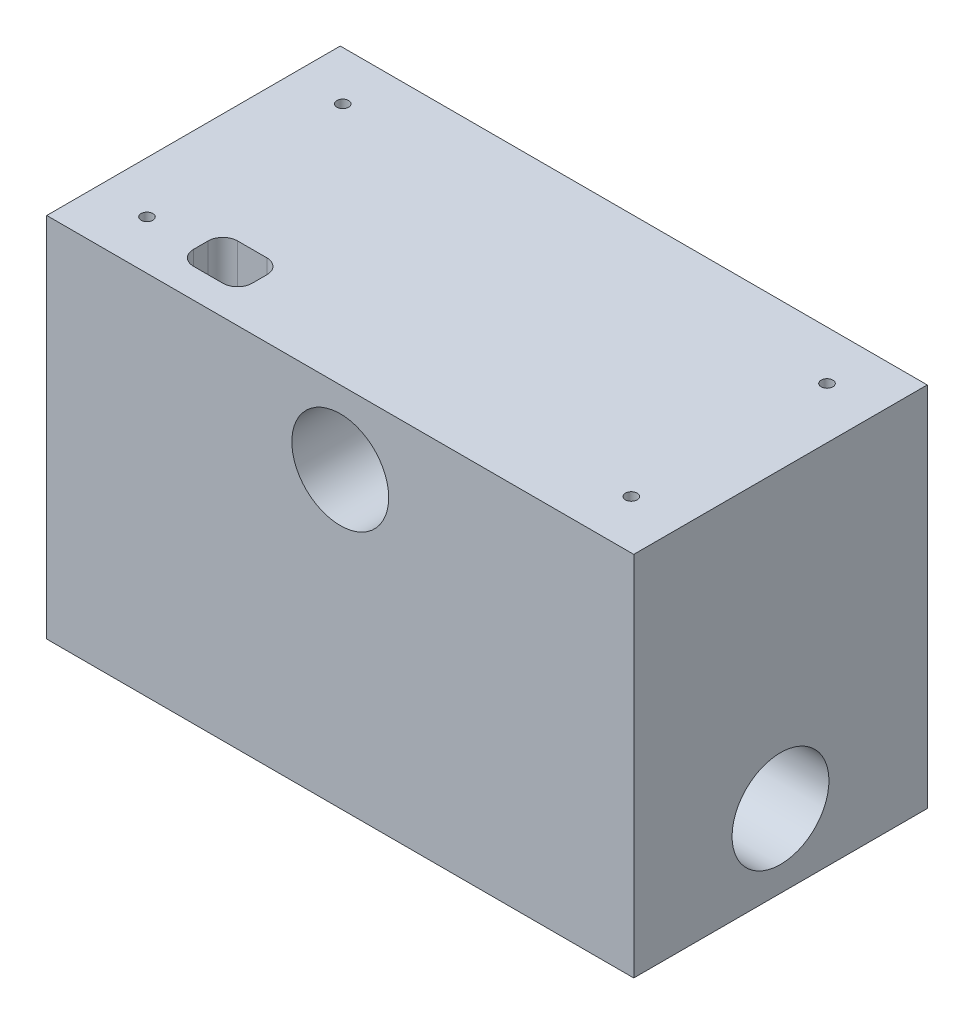
SolidWorks part; units mm, degrees
ref_plane "Front Plane" through (0, 0, 0) normal (0, 0, 1) x (1, 0, 0)
ref_plane "Top Plane" through (0, 0, 0) normal (0, 1, 0) x (1, 0, 0)
ref_plane "Right Plane" through (0, 0, 0) normal (1, 0, 0) x (0, 0, -1)
sketch "Sketch1" plane through (0, 0, 0) normal (0, 0, 1) x (1, 0, 0)
  line L1 (-25.4, 15.875) -> (25.4, 15.875)
  line L2 (-25.4, 15.875) -> (-25.4, -15.875)
  line L3 (-25.4, -15.875) -> (25.4, -15.875)
  line L4 (25.4, 15.875) -> (25.4, -15.875)
  line L5 (-25.4, 15.875) -> (25.4, -15.875) construction
  line L6 (-25.4, -15.875) -> (25.4, 15.875) construction
  point P0 (0, 0)
  dimension "D1" = 50.8
  dimension "D2" = 31.75
extrude "Boss-Extrude1" add sketch "Sketch1" along normal blind 25.4
sketch "Sketch4" plane through (-25.4, 0, 0) normal (-1, 0, 0) x (0, 0, 1)
  line L0 (0, 15.875) -> (0, -15.875) construction
  line L1 (25.4, -15.875) -> (0, -15.875) construction
  circle A0 centre (12.7, -9.525) radius 4.191
  dimension "D1" = 8.382
  dimension "D2" = 12.7
  dimension "D3" = 6.35
extrude "Cut-Extrude1" cut sketch "Sketch4" against normal blind 152.4
sketch "Sketch5" plane through (0, 0, 25.4) normal (0, 0, 1) x (1, 0, 0)
  line L0 (25.4, 15.875) -> (-25.4, 15.875) construction
  circle A0 centre (0, 9.525) radius 4.191
  dimension "D1" = 8.382
  dimension "D2" = 6.35
extrude "Cut-Extrude2" cut sketch "Sketch5" against normal up to vertex (25.4 mm away) up to point (0, 0, 0)
sketch "Sketch7" plane through (0, 15.875, 0) normal (0, 1, 0) x (1, 0, 0)
  line L0 (-25.4, -25.4) -> (-25.4, 0) construction
  circle A0 centre (-20.955, -4.2291) radius 0.508
  circle A1 centre (-20.955, -21.1709) radius 0.508
  circle A2 centre (20.955, -4.2291) radius 0.508
  circle A3 centre (20.955, -21.1709) radius 0.508
  point P4 (-25.4, -12.7)
  dimension "D3" = 1.016
  dimension "D4" = 41.91
  dimension "D5" = 20.955
  dimension "D1" = 16.9418
  dimension "D2" = 8.4709
extrude "Cut-Extrude3" cut sketch "Sketch7" against normal blind 7.62
sketch "Sketch9" plane through (0, 15.875, 0) normal (0, 1, 0) x (1, 0, 0)
  line L0 (25.4, -25.4) -> (-25.4, -25.4) construction
  line L1 (-16.51, -19.05) -> (-11.43, -19.05)
  line L2 (-16.51, -19.05) -> (-16.51, -22.86)
  line L3 (-16.51, -22.86) -> (-11.43, -22.86)
  line L4 (-11.43, -19.05) -> (-11.43, -22.86)
  line L5 (-25.4, -25.4) -> (-25.4, 0) construction
  point P6 (-25.4, -12.7)
  dimension "D1" = 5.08
  dimension "D2" = 3.81
  dimension "D3" = 2.54
  dimension "D4" = 3.81
  dimension "D5" = 8.89
extrude "Cut-Extrude5" cut sketch "Sketch9" against normal blind 152.4
fillet "Fillet1" radius 1.27 4 edges at (-11.43, 0, 19.05) (-16.51, 0, 19.05) (-16.51, 0, 22.86) (-11.43, 0, 22.86)
